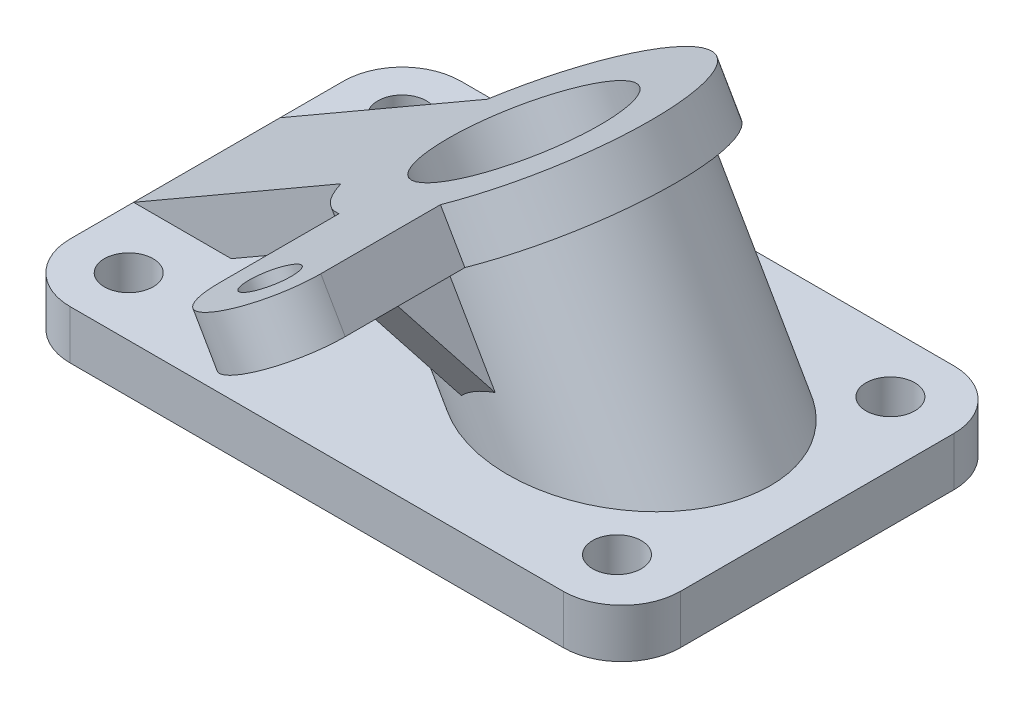
SolidWorks part; units mm, degrees
ref_plane "前视基准面" through (0, 0, 0) normal (0, 0, 1) x (1, 0, 0)
ref_plane "上视基准面" through (0, 0, 0) normal (0, 1, 0) x (1, 0, 0)
ref_plane "右视基准面" through (0, 0, 0) normal (1, 0, 0) x (0, 0, -1)
sketch "草图1" plane through (0, 0, 0) normal (0, 1, 0) x (1, 0, 0)
  line L1 (-69.7085, 31.2976) -> (31.2915, 31.2976)
  line L2 (-81.7085, 19.2976) -> (-81.7085, -36.7024)
  line L3 (-69.7085, -48.7024) -> (31.2915, -48.7024)
  line L4 (43.2915, 19.2976) -> (43.2915, -36.7024)
  arc A0 (-69.7085, 31.2976) -> (-81.7085, 19.2976) centre (-69.7085, 19.2976) ccw
  arc A1 (43.2915, 19.2976) -> (31.2915, 31.2976) centre (31.2915, 19.2976) ccw
  arc A2 (31.2915, -48.7024) -> (43.2915, -36.7024) centre (31.2915, -36.7024) ccw
  arc A3 (-81.7085, -36.7024) -> (-69.7085, -48.7024) centre (-69.7085, -36.7024) ccw
  circle A4 centre (-69.7085, -36.7024) radius 5
  circle A5 centre (30.2915, -36.7024) radius 5
  circle A6 centre (30.2915, 19.2976) radius 5
  circle A7 centre (-69.7085, 19.2976) radius 5
  dimension "D1" = 2
  dimension "D2" = 2
extrude "凸台-拉伸1" add sketch "草图1" along normal blind 10
ref_plane "基准面1" through (-20.4271, 35.3808, 0) normal (-0.5, 0.866, 0) x (0, 0, 1)
ref_plane "基准面2" through (-24.7573, 42.8808, 0) normal (-0.5, 0.866, 0) x (0, 0, 1)
sketch "草图3" plane through (-24.7573, 42.8808, 0) normal (-0.5, 0.866, 0) x (0, 0, 1)
  line L6 (-19.2976, -65.7616) -> (36.7024, -65.7616) construction
  line L7 (-6.2976, -65.7616) -> (-6.2976, -16.7424)
  line L8 (-6.2976, -65.7616) -> (23.7024, -65.7616)
  line L10 (36.1978, -2.7616) -> (60.7024, -2.7616)
  line L11 (23.7024, -65.7616) -> (23.7024, -16.7424)
  line L12 (36.1978, 21.2384) -> (60.7024, 21.2384)
  arc A5 (60.7024, 21.2384) -> (60.7024, -2.7616) centre (60.7024, 9.2384) cw
  circle A6 centre (60.7024, 9.2384) radius 5
  circle A7 centre (8.7024, 9.2384) radius 18
  arc A8 (23.7024, -16.7424) -> (36.1978, -2.7616) centre (8.7024, 9.2384) ccw
  arc A9 (36.1978, 21.2384) -> (-6.2976, -16.7424) centre (8.7024, 9.2384) ccw
  point P17 (8.7024, -65.7616)
  point P33 (37.8215, -59.8052)
  point P34 (37.8215, -59.8052)
  point P35 (8.7024, -65.7616)
extrude "凸台-拉伸3" add sketch "草图3" against normal blind 10
sketch "草图4" plane through (-24.7573, 42.8808, 0) normal (-0.5, 0.866, 0) x (0, 0, 1)
  circle A0 centre (8.7024, 9.2384) radius 25
extrude "凸台-拉伸4" add sketch "草图4" against normal up to next contours A0
sketch "草图5" plane through (-24.7573, 42.8808, 0) normal (-0.5, 0.866, 0) x (0.866, 0.5, 0)
  circle A0 centre (9.2384, -8.7024) radius 18
extrude "切除-拉伸1" cut sketch "草图5" against normal through all
sketch "草图6" plane through (-24.7573, 42.8808, 0) normal (-0.5, 0.866, 0) x (0, 0, 1)
  line L0 (8.7024, 9.2384) -> (60.7024, 9.2384)
ref_plane "基准面3" through (8.0007, 4.6192, 0) normal (-0.866, -0.5, 0) x (0, 0, 1)
sketch "草图7" plane through (8.0007, 4.6192, 0) normal (-0.866, -0.5, 0) x (0, 0, 1)
  line L0 (45.2977, 39.5145) -> (30.0119, 39.5145)
  line L1 (45.2977, 39.5145) -> (30.4723, 13.8362)
  line L3 (30.0119, 39.5145) -> (30.4723, 13.8362)
extrude "凸台-拉伸6" add sketch "草图7" along normal mid plane 8 contours L1 L3 L0
